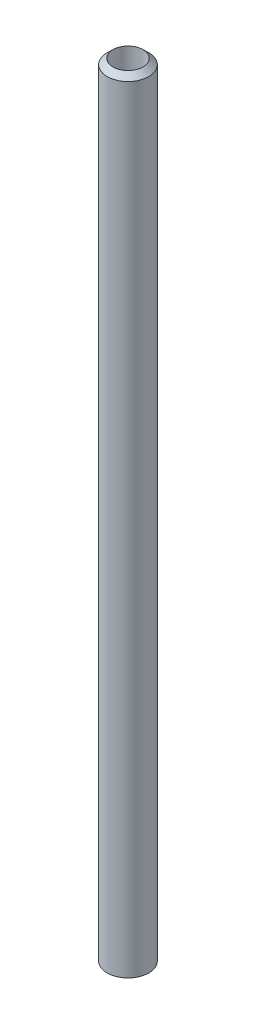
SolidWorks part; units mm, degrees
ref_plane "Front Plane" through (0, 0, 0) normal (0, 0, 1) x (1, 0, 0)
ref_plane "Top Plane" through (0, 0, 0) normal (0, 1, 0) x (1, 0, 0)
ref_plane "Right Plane" through (0, 0, 0) normal (1, 0, 0) x (0, 0, -1)
sketch "Sketch1" plane through (0, 0, 0) normal (0, 1, 0) x (1, 0, 0)
  circle A0 centre (0, 0) radius 4.826
  dimension "D1" = 9.652
extrude "Boss-Extrude1" add sketch "Sketch1" along normal blind 180.34
sketch "Sketch2" plane through (0, 180.34, 0) normal (0, 1, 0) x (1, 0, 0)
  circle A0 centre (0, 0) radius 3.4925
  dimension "D1" = 6.985
extrude "Boss-Extrude2" add sketch "Sketch2" along normal blind 1.27
loft "Loft3" add section face at (0, 181.61, 3.4925) section edge at (0, 180.34, 4.826)
sketch "Sketch3" plane through (0, 181.61, 0) normal (0, 1, 0) x (1, 0, 0)
  circle A0 centre (0, 0) radius 3.4912
  dimension "D1" = 6.9825
extrude "Cut-Extrude2" cut sketch "Sketch3" against normal blind 203.2
